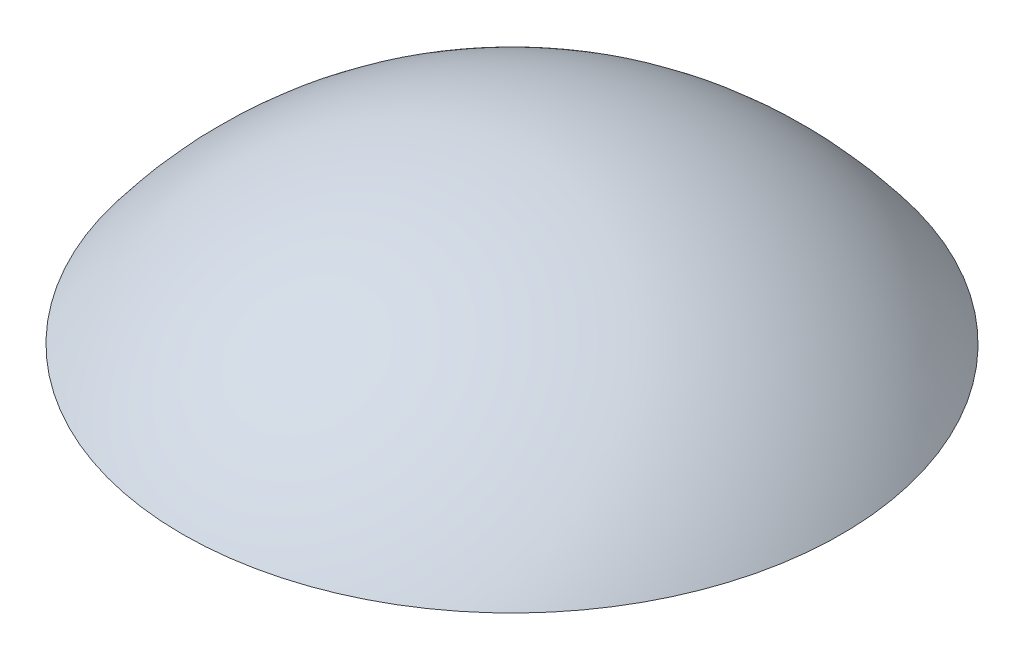
SolidWorks part; units mm, degrees
material "ABS"
ref_plane "Front Plane" through (0, 0, 0) normal (0, 0, 1) x (1, 0, 0)
ref_plane "Top Plane" through (0, 0, 0) normal (0, 1, 0) x (1, 0, 0)
ref_plane "Right Plane" through (0, 0, 0) normal (1, 0, 0) x (0, 0, -1)
sketch "Sketch1" plane through (0, 0, 0) normal (1, 0, 0) x (0, 0, -1)
  line L5 (25.4, 0) -> (0, 0)
  line L7 (0, 12.7) -> (0, 0)
  line L8 (0, 12.7) -> (-10, 12.7) construction
  arc A1 (25.4, 0) -> (0, 12.7) centre (0, -19.05) ccw
  dimension "D5" = 25.4
  dimension "D1" = 12.7
  dimension "D2" = 10
  dimension "D3" = 90
ref_axis "Axis1" through (0, 12.7, 0) along (0, -1, 0)
revolve "Revolve1" add sketch "Sketch1" angle 360 about axis through (0, 12.7, 0) along (0, -1, 0)
equation "\"D5@Sketch1\"=1in"
equation "\"D1@Sketch1\"=.5in"
